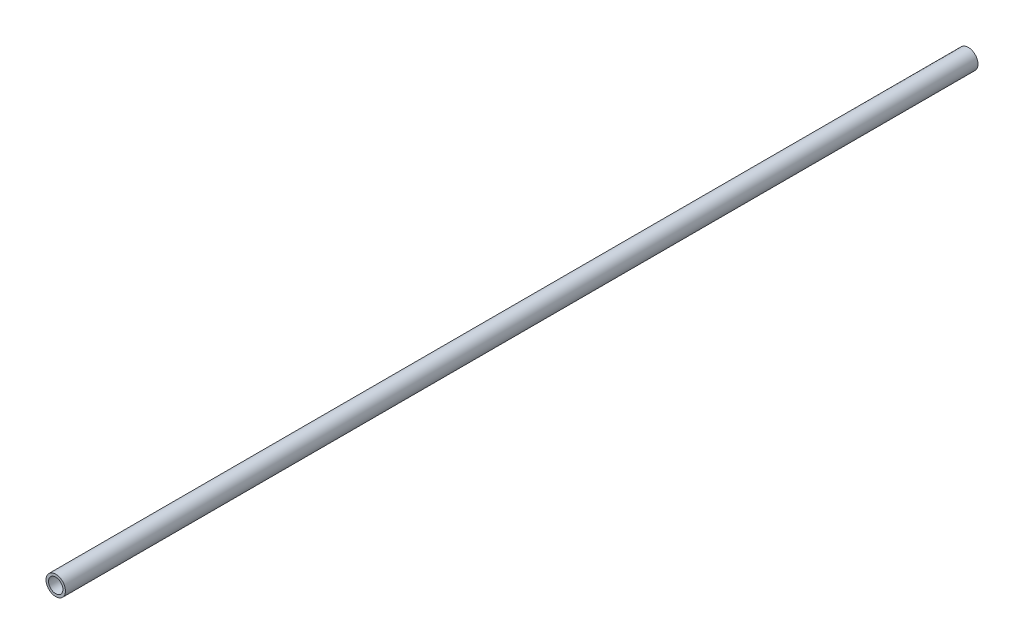
SolidWorks part; units mm, degrees
ref_plane "Front Plane" through (0, 0, 0) normal (0, 0, 1) x (1, 0, 0)
ref_plane "Top Plane" through (0, 0, 0) normal (0, 1, 0) x (1, 0, 0)
ref_plane "Right Plane" through (0, 0, 0) normal (1, 0, 0) x (0, 0, -1)
sketch "Sketch1" plane through (0, 0, 0) normal (0, 0, 1) x (1, 0, 0)
  circle A0 centre (0, 0) radius 10.668
  dimension "Pipe OD" = 21.336
extrude "Extrude-Thin1" add sketch "Sketch1" along normal mid plane 1000 thin thin type one direction reverse wall 2.7686
